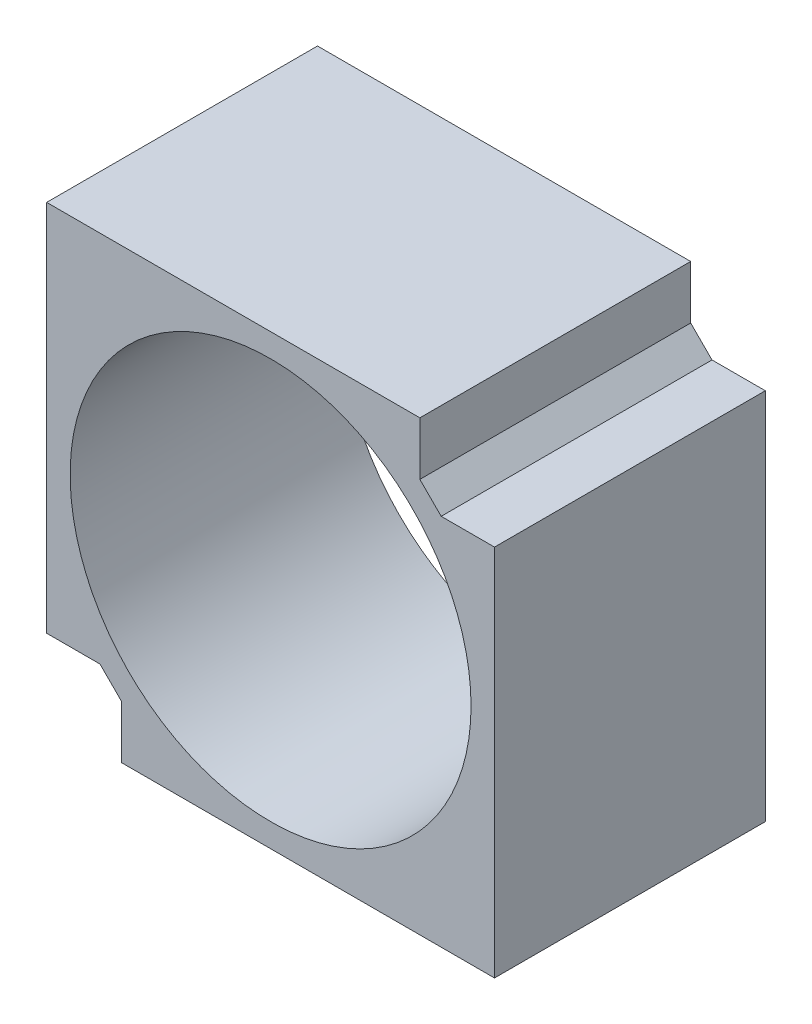
SolidWorks part; units mm, degrees
ref_plane "Front Plane" through (0, 0, 0) normal (0, 0, 1) x (1, 0, 0)
ref_plane "Top Plane" through (0, 0, 0) normal (0, 1, 0) x (1, 0, 0)
ref_plane "Right Plane" through (0, 0, 0) normal (1, 0, 0) x (0, 0, -1)
sketch "Sketch1" plane through (0, 0, 0) normal (0, 0, 1) x (1, 0, 0)
  line L0 (0, 0) -> (0, 21) construction
  line L1 (0, 21) -> (21, 21)
  line L2 (21, 21) -> (21, -21)
  line L3 (21, -21) -> (-21, -21)
  line L6 (-21, -21) -> (-21, 21)
  line L7 (-21, 21) -> (0, 21)
  dimension "D1" = 21
  dimension "D2" = 21
  dimension "D3" = 21
  dimension "D4" = 42
extrude "Boss-Extrude1" add sketch "Sketch1" along normal blind 25.4
sketch "Sketch2" plane through (0, 0, 25.4) normal (0, 0, 1) x (1, 0, 0)
  line L0 (21, 21) -> (21, 14)
  line L1 (21, -21) -> (21, 21) construction
  line L2 (21, 14) -> (16, 14)
  line L7 (16, 14) -> (14, 16)
  line L8 (14, 16) -> (14, 21)
  line L9 (21, 21) -> (-21, 21) construction
  line L10 (14, 21) -> (21, 21)
  dimension "D1" = 2
  dimension "D2" = 5
  dimension "D3" = 2
extrude "Cut-Extrude1" cut sketch "Sketch2" against normal blind 25.4
sketch "Sketch3" plane through (0, 0, 25.4) normal (0, 0, 1) x (1, 0, 0)
  line L0 (-14, -16) -> (-16, -14)
  line L1 (-21, -21) -> (21, -21) construction
  line L2 (-14, -21) -> (-14, -16)
  line L3 (-16, -14) -> (-21, -14)
  line L4 (-21, 21) -> (-21, -21) construction
  line L5 (-21, -14) -> (-21, -21)
  line L6 (-21, -21) -> (-14, -21)
  dimension "D1" = 5
  dimension "D2" = 2
  dimension "D3" = 2
  dimension "D4" = 5
extrude "Cut-Extrude2" cut sketch "Sketch3" against normal blind 25.4
sketch "Sketch4" plane through (0, 0, 25.4) normal (0, 0, 1) x (1, 0, 0)
  circle A0 centre (0, 0) radius 18.8
  dimension "D1" = 37.6
extrude "Cut-Extrude3" cut sketch "Sketch4" against normal blind 25.4
